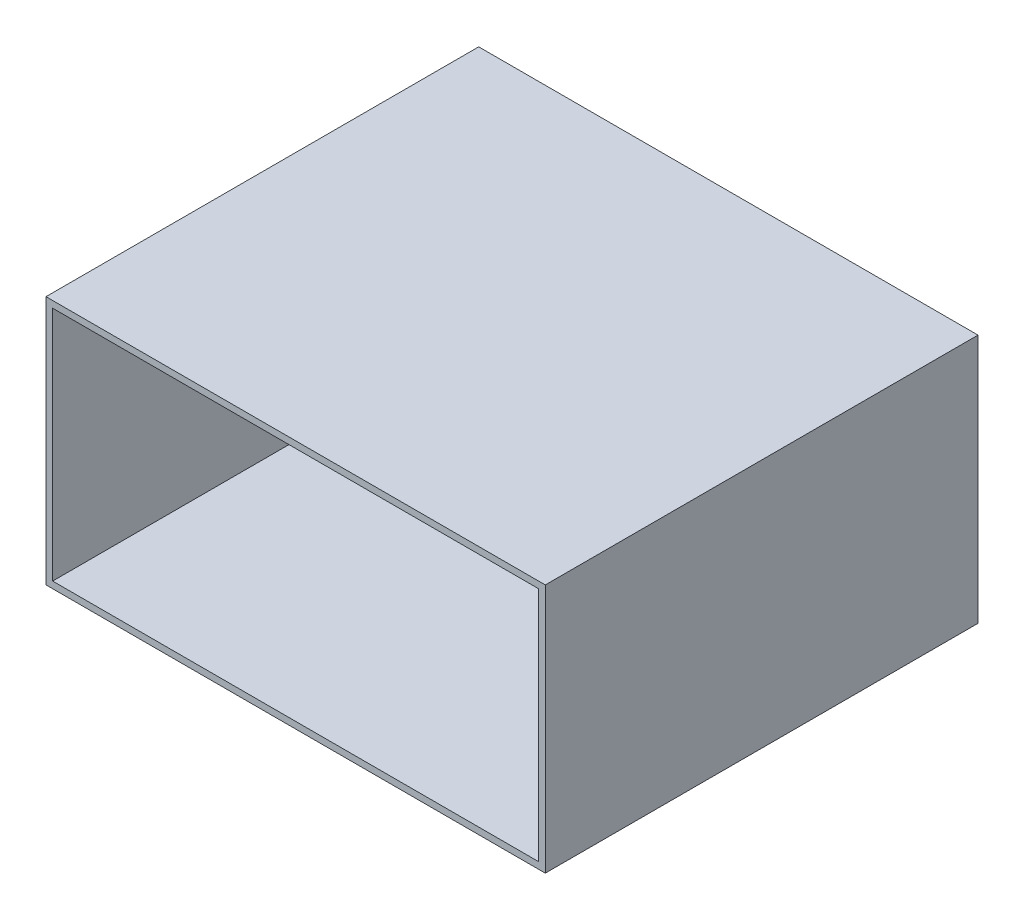
SolidWorks part; units mm, degrees
ref_plane "Front Plane" through (0, 0, 0) normal (0, 0, 1) x (1, 0, 0)
ref_plane "Top Plane" through (0, 0, 0) normal (0, 1, 0) x (1, 0, 0)
ref_plane "Right Plane" through (0, 0, 0) normal (1, 0, 0) x (0, 0, -1)
sketch "Sketch1" plane through (0, 0, 0) normal (0, 0, 1) x (1, 0, 0)
  line L0 (-365, 177.5) -> (365, 177.5)
  line L1 (-375, -187.5) -> (375, -187.5)
  line L2 (-375, -187.5) -> (-375, 187.5)
  line L3 (-375, 187.5) -> (375, 187.5)
  line L4 (375, -187.5) -> (375, 187.5)
  line L5 (-375, -187.5) -> (375, 187.5) construction
  line L6 (-375, 187.5) -> (375, -187.5) construction
  line L7 (365, -177.5) -> (365, 177.5)
  line L8 (-365, -177.5) -> (365, -177.5)
  line L9 (-365, -177.5) -> (-365, 177.5)
  point P0 (0, 0)
  dimension "D1" = 750
  dimension "D2" = 375
  dimension "D3" = 10
extrude "Boss-Extrude2" add sketch "Sketch1" along normal blind 650
